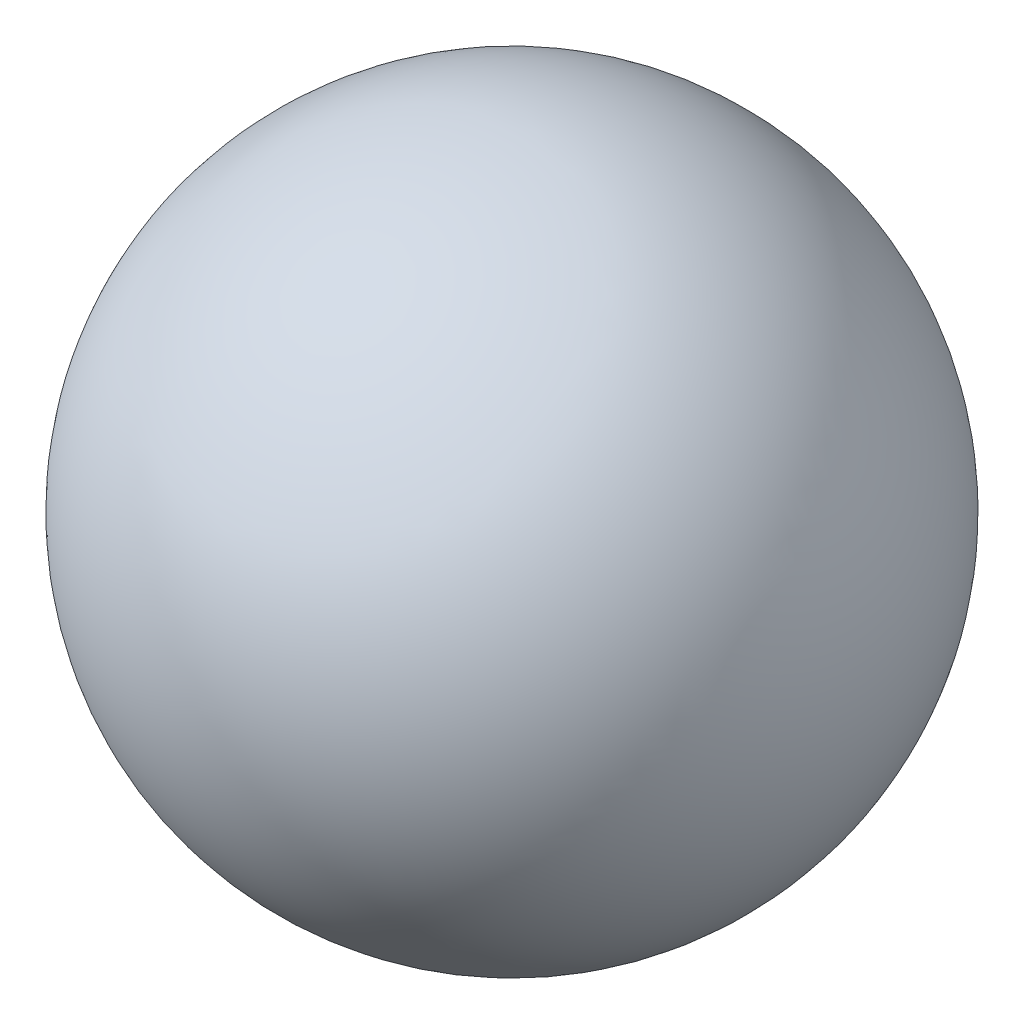
SolidWorks part; units mm, degrees
ref_plane "Front Plane" through (0, 0, 0) normal (0, 0, 1) x (1, 0, 0)
ref_plane "Top Plane" through (0, 0, 0) normal (0, 1, 0) x (1, 0, 0)
ref_plane "Right Plane" through (0, 0, 0) normal (1, 0, 0) x (0, 0, -1)
sketch "Sketch1" plane through (0, 0, 0) normal (0, 0, 1) x (1, 0, 0)
  line L2 (-15.2756, 0) -> (17.7925, 0) construction
  line L3 (-6.35, 0) -> (6.35, 0)
  arc A1 (6.35, 0) -> (-6.35, 0) centre (0, 0) ccw
  dimension "D1" = 6.35
revolve "Revolve1" add sketch "Sketch1" angle 360 about L2
